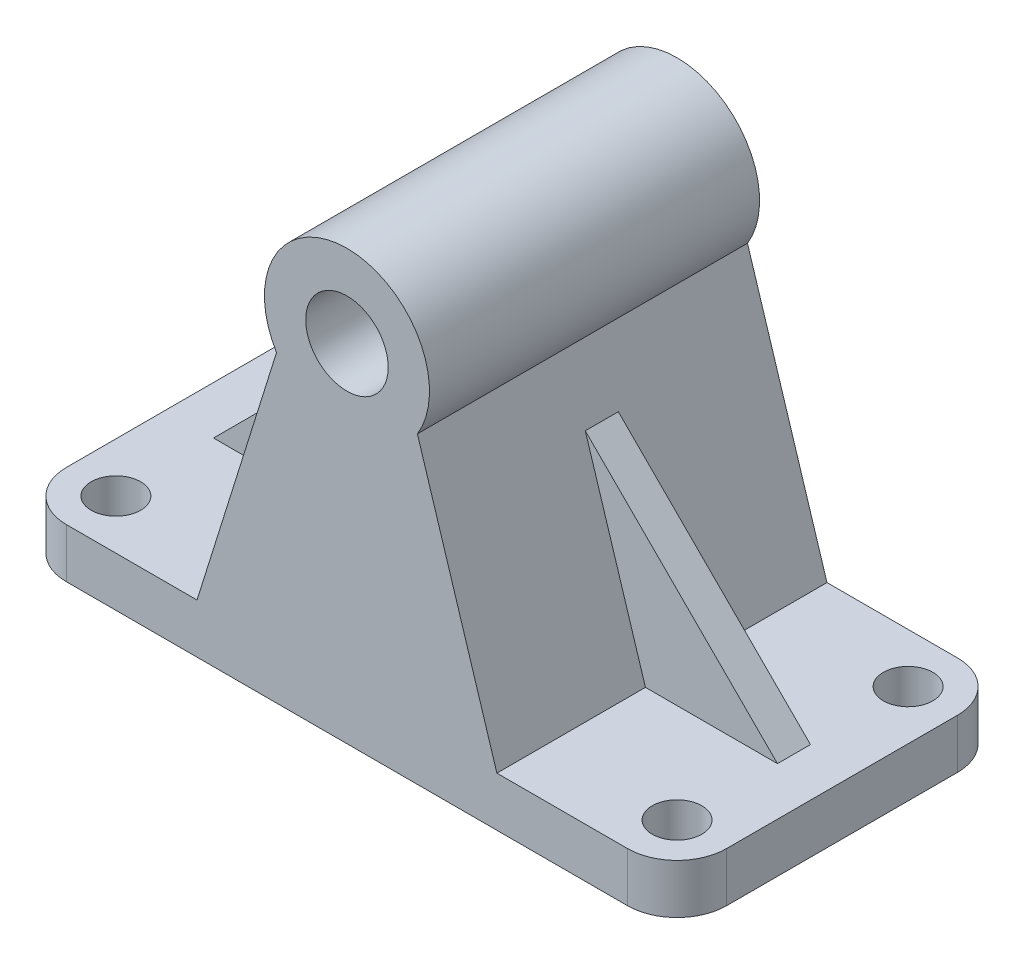
SolidWorks part; units mm, degrees
ref_plane "Front Plane" through (0, 0, 0) normal (0, 0, 1) x (1, 0, 0)
ref_plane "Top Plane" through (0, 0, 0) normal (0, 1, 0) x (1, 0, 0)
ref_plane "Right Plane" through (0, 0, 0) normal (1, 0, 0) x (0, 0, -1)
sketch "Sketch1" plane through (0, 0, 0) normal (0, 1, 0) x (1, 0, 0)
  line L1 (85, -50) -> (-85, -50)
  line L2 (100, -35) -> (100, 35)
  line L3 (85, 50) -> (-85, 50)
  line L4 (-100, -35) -> (-100, 35)
  line L5 (100, -50) -> (-100, 50) construction
  line L6 (100, 50) -> (-100, -50) construction
  arc A0 (-100, 35) -> (-85, 50) centre (-85, 35) cw
  arc A1 (-85, -50) -> (-100, -35) centre (-85, -35) cw
  arc A2 (100, -35) -> (85, -50) centre (85, -35) cw
  arc A3 (100, 35) -> (85, 50) centre (85, 35) ccw
  point P0 (0, 0)
  dimension "D3" = 15
  dimension "D4" = 15
  dimension "D5" = 15
  dimension "D6" = 15
  dimension "D1" = 200
  dimension "D2" = 100
extrude "Boss-Extrude1" add sketch "Sketch1" along normal blind 15
sketch "Sketch2" plane through (0, 15, 0) normal (0, 1, 0) x (1, 0, 0)
  circle A0 centre (-85, 35) radius 7.5
  circle A1 centre (-85, -35) radius 7.5
  circle A2 centre (85, -35) radius 7.5
  circle A3 centre (85, 35) radius 7.5
extrude "Cut-Extrude1" cut sketch "Sketch2" against normal blind 15
sketch "Sketch3" plane through (0, 0, 0) normal (0, 0, 1) x (1, 0, 0)
  line L0 (-85, 15) -> (85, 15) construction
  line L1 (-45.4242, 15) -> (-21.3363, 91.9707)
  line L2 (0, 105) -> (0, -25.0372) construction
  line L3 (45.4242, 15) -> (21.3363, 91.9707)
  line L4 (-45.4242, 15) -> (45.4242, 15)
  arc A0 (21.3363, 91.9707) -> (-21.3363, 91.9707) centre (0, 105) ccw
  dimension "D1" = 90
  dimension "D2" = 50
extrude "Boss-Extrude2" add sketch "Sketch3" along normal mid plane 100
sketch "Sketch4" plane through (0, 0, 0) normal (0, 0, 1) x (1, 0, 0)
  circle A0 centre (0, 105) radius 12.5
extrude "Cut-Extrude2" cut sketch "Sketch4" against normal mid plane 100
sketch "Sketch6" plane through (0, 0, 0) normal (0, 0, 1) x (1, 0, 0)
  line L0 (-85.4242, 15) -> (-27.2044, 73.2198)
  line L1 (-85, 15) -> (-45.4242, 15) construction
  line L2 (-21.3363, 91.9707) -> (-45.4242, 15) construction
  line L3 (-85.4242, 15) -> (-45.4242, 15)
  line L4 (-45.4242, 15) -> (-27.2044, 73.2198)
  line L5 (0, 105) -> (0, -22.5452) construction
  line L6 (45.4242, 15) -> (27.2044, 73.2198)
  line L7 (85.4242, 15) -> (45.4242, 15)
  line L8 (85.4242, 15) -> (27.2044, 73.2198)
  dimension "D1" = 40
extrude "Boss-Extrude3" add sketch "Sketch6" along normal mid plane 10
